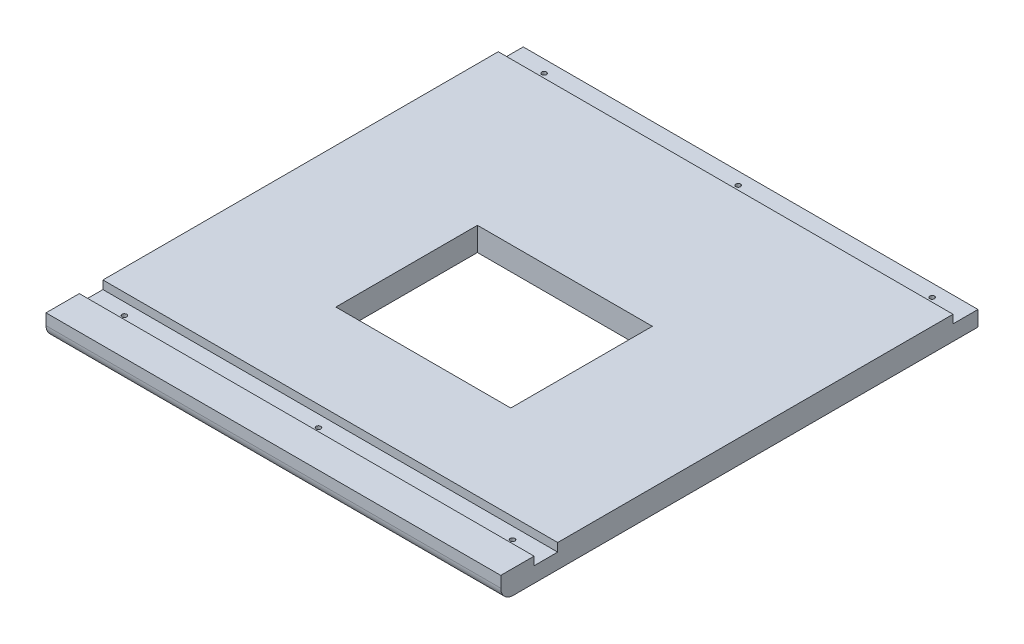
SolidWorks part; units mm, degrees
ref_plane "Front Plane" through (0, 0, 0) normal (0, 0, 1) x (1, 0, 0)
ref_plane "Top Plane" through (0, 0, 0) normal (0, 1, 0) x (1, 0, 0)
ref_plane "Right Plane" through (0, 0, 0) normal (1, 0, 0) x (0, 0, -1)
sketch "Sketch1" plane through (0, 0, 0) normal (0, 1, 0) x (1, 0, 0)
  line L1 (0, 0) -> (346.7, 0)
  line L2 (0, 0) -> (0, -376.55)
  line L3 (0, -376.55) -> (346.7, -376.55)
  line L4 (346.7, 0) -> (346.7, -376.55)
  dimension "D1" = 346.7
  dimension "D2" = 376.55
extrude "Boss-Extrude1" add sketch "Sketch1" along normal blind 18
sketch "Sketch2" plane through (0, 18, 0) normal (0, 1, 0) x (1, 0, 0)
  line L0 (0, -376.55) -> (346.7, -376.55) construction
  line L1 (346.7, -338.45) -> (0, -338.45)
  line L2 (346.7, -338.45) -> (346.7, -320.45)
  line L3 (346.7, -320.45) -> (0, -320.45)
  line L4 (0, -338.45) -> (0, -320.45)
  line L5 (0, 0) -> (0, -376.55) construction
  line L6 (346.7, -376.55) -> (346.7, 0) construction
  dimension "D1" = 18
  dimension "D2" = 38.1
  dimension "D3" = 0
  dimension "D4" = 0
extrude "Cut-Extrude1" cut sketch "Sketch2" against normal blind 6.35
sketch "Sketch3" plane through (0, 18, 0) normal (0, 1, 0) x (1, 0, 0)
  line L0 (0, -376.55) -> (346.7, -376.55) construction
  line L1 (106.675, -249.55) -> (240.025, -249.55)
  line L2 (106.675, -249.55) -> (106.675, -141.6)
  line L3 (106.675, -141.6) -> (240.025, -141.6)
  line L4 (240.025, -249.55) -> (240.025, -141.6)
  point P7 (173.35, -249.55)
  point P8 (173.35, -376.55)
  point P9 (106.675, -195.575)
  dimension "D1" = 107.95
  dimension "D2" = 133.35
  dimension "D3" = 0
  dimension "D4" = 180.975
extrude "Cut-Extrude3" cut sketch "Sketch3" against normal through all
fillet "Fillet1" radius 9.525 1 edges at (173.35, 0, 376.55)
sketch "Sketch6" plane through (0, 18, 0) normal (0, 1, 0) x (1, 0, 0)
  line L0 (346.7, -320.45) -> (346.7, 0) construction
  line L1 (0, 0) -> (346.7, 0)
  line L2 (0, 0) -> (0, -19.05)
  line L3 (0, -19.05) -> (346.7, -19.05)
  line L4 (346.7, 0) -> (346.7, -19.05)
  dimension "D1" = 19.05
extrude "Cut-Extrude4" cut sketch "Sketch6" against normal up to surface (6.35 mm away) up to face at (173.35, 11.65, 329.45)
sketch "Sketch7" plane through (0, 18, 0) normal (0, 1, 0) x (1, 0, 0)
  line L1 (0, -376.55) -> (346.7, -376.55)
  line L2 (0, -376.55) -> (0, -363.85)
  line L3 (0, -363.85) -> (346.7, -363.85)
  line L4 (346.7, -376.55) -> (346.7, -363.85)
  dimension "D1" = 12.7
extrude "Cut-Extrude5" cut sketch "Sketch7" against normal through all
fillet "Fillet2" radius 9.525 1 edges at (173.35, 0, 363.85)
sketch "Sketch8" plane through (0, 11.65, 0) normal (0, 1, 0) x (1, 0, 0)
  line L0 (173.35, 0) -> (173.35, -449.9968) construction
  line L1 (0, 0) -> (346.7, 0) construction
  line L3 (25.4, 20.153) -> (25.4, -383.3098) construction
  line L4 (321.3, 20.153) -> (321.3, -383.3098) construction
  line L5 (0, -9.525) -> (413.1787, -9.525) construction
  line L6 (0, -329.45) -> (346.7, -329.45) construction
  line L7 (0, -320.45) -> (0, -338.45) construction
  line L8 (346.7, -338.45) -> (346.7, -320.45) construction
  line L10 (0, -19.05) -> (0, 0) construction
  line L11 (0, -19.05) -> (0, -320.45) construction
  circle A0 centre (173.35, -9.525) radius 1.7859
  circle A1 centre (173.35, -329.45) radius 1.7859
  circle A2 centre (25.4, -329.45) radius 1.7859
  circle A3 centre (321.3, -329.45) radius 1.7859
  circle A4 centre (321.3, -9.525) radius 1.7859
  circle A5 centre (25.4, -9.525) radius 1.7859
  dimension "D1" = 3.5719
  dimension "D2" = 25.4
extrude "Cut-Extrude6" cut sketch "Sketch8" against normal through all
